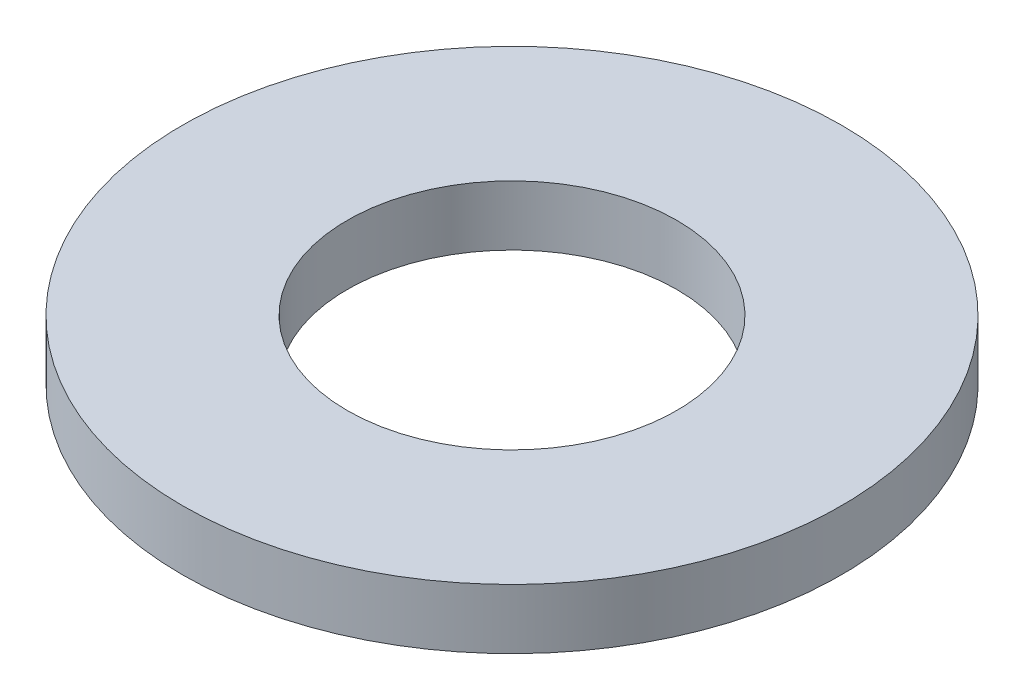
SolidWorks part; units mm, degrees
material "1.4057 (X17CrNi16-2)"
ref_plane "Plano frontal" through (0, 0, 0) normal (0, 0, 1) x (1, 0, 0)
ref_plane "Plano superior" through (0, 0, 0) normal (0, 1, 0) x (1, 0, 0)
ref_plane "Plano direito" through (0, 0, 0) normal (1, 0, 0) x (0, 0, -1)
sketch "Esboço1" plane through (0, 0, 0) normal (0, 1, 0) x (1, 0, 0)
  circle A0 centre (0, 0) radius 4.4
  circle A1 centre (0, 0) radius 2.2
  dimension "D1" = 4.4
  dimension "D2" = 8.8
extrude "Ressalto-extrusão1" add sketch "Esboço1" along normal blind 0.8
